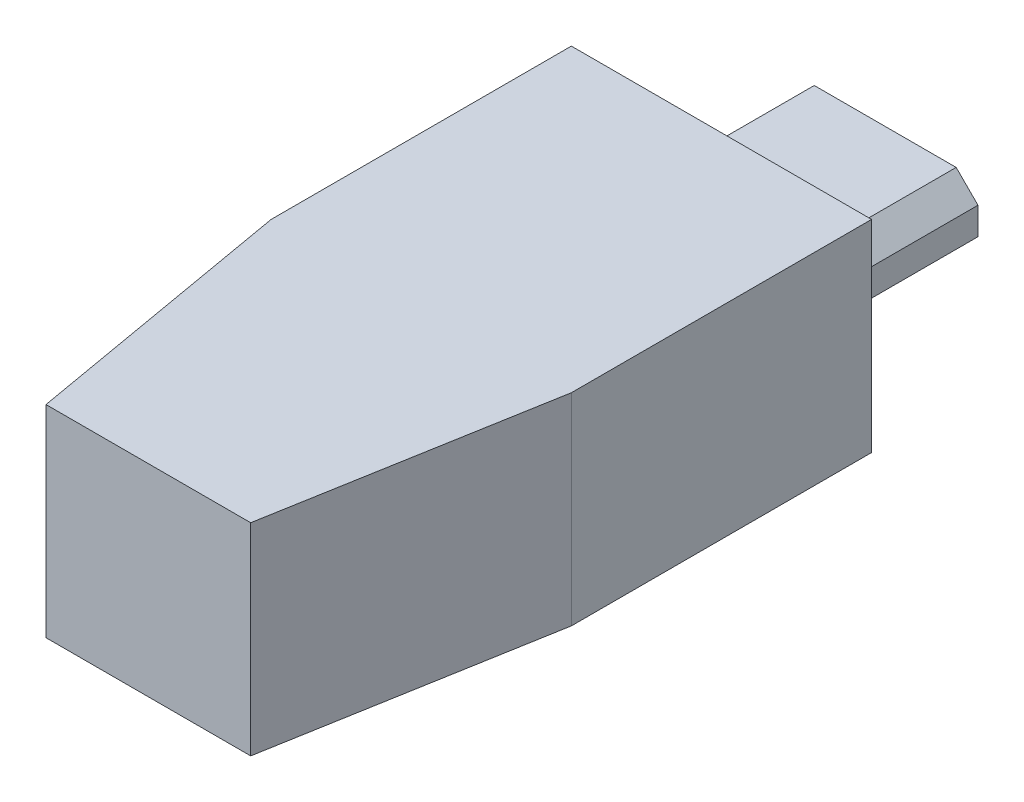
SolidWorks part; units mm, degrees
ref_plane "Front Plane" through (0, 0, 0) normal (0, 0, 1) x (1, 0, 0)
ref_plane "Top Plane" through (0, 0, 0) normal (0, 1, 0) x (1, 0, 0)
ref_plane "Right Plane" through (0, 0, 0) normal (1, 0, 0) x (0, 0, -1)
sketch "Skica1" plane through (0, 0, 0) normal (0, 0, 1) x (1, 0, 0)
  line L1 (-5.5, 3.7) -> (5.5, 3.7)
  line L2 (-5.5, 3.7) -> (-5.5, -3.7)
  line L3 (-5.5, -3.7) -> (5.5, -3.7)
  line L4 (5.5, 3.7) -> (5.5, -3.7)
  line L5 (-5.5, 3.7) -> (5.5, -3.7) construction
  line L6 (-5.5, -3.7) -> (5.5, 3.7) construction
  point P0 (0, 0)
  dimension "D1" = 7.4
  dimension "D2" = 11
extrude "Přidat vysunutím1" add sketch "Skica1" along normal blind 21
sketch "Skica2" plane through (0, 3.7, 0) normal (0, 1, 0) x (1, 0, 0)
  line L0 (-5.5, -11) -> (-3.75, -21)
  line L1 (-5.5, -21) -> (-5.5, 0) construction
  line L2 (5.5, -21) -> (-5.5, -21) construction
  line L3 (-3.75, -21) -> (3.75, -21)
  line L4 (3.75, -21) -> (5.5, -11)
  line L5 (5.5, -21) -> (5.5, 0) construction
  line L6 (5.5, -11) -> (8.0218, -11)
  line L7 (8.0218, -11) -> (9.221, -26.1899)
  line L8 (9.221, -26.1899) -> (-8.6472, -26.1899)
  line L9 (-8.6472, -26.1899) -> (-5.5, -11)
  line L10 (5.5, 0) -> (-5.5, 0) construction
  point P16 (0, 0)
  dimension "D1" = 7.5
  dimension "D2" = 11
  dimension "D3" = 1.75
extrude "Odebrat vysunutím1" cut sketch "Skica2" against normal blind 21
sketch "Skica3" plane through (0, 0, 0) normal (0, 0, -1) x (-1, 0, 0)
  line L0 (-3.4, 0.1) -> (-2.6, 0.9)
  line L1 (-2.6, 0.9) -> (2.6, 0.9)
  line L2 (-3.4, 0.1) -> (-3.4, -0.9)
  line L3 (-3.4, -0.9) -> (3.4, -0.9)
  line L4 (3.4, 0.1) -> (3.4, -0.9)
  line L5 (-2.7674, 0.7326) -> (3.4, -0.9) construction
  line L6 (-3.4, -0.9) -> (3.4, 0.9) construction
  line L7 (2.6, 0.9) -> (3.4, 0.1)
  point P0 (0, 0)
  point P2 (0, 0)
  dimension "D1" = 1.8
  dimension "D4" = 45
extrude "Přidat vysunutím2" add sketch "Skica3" along normal blind 6
